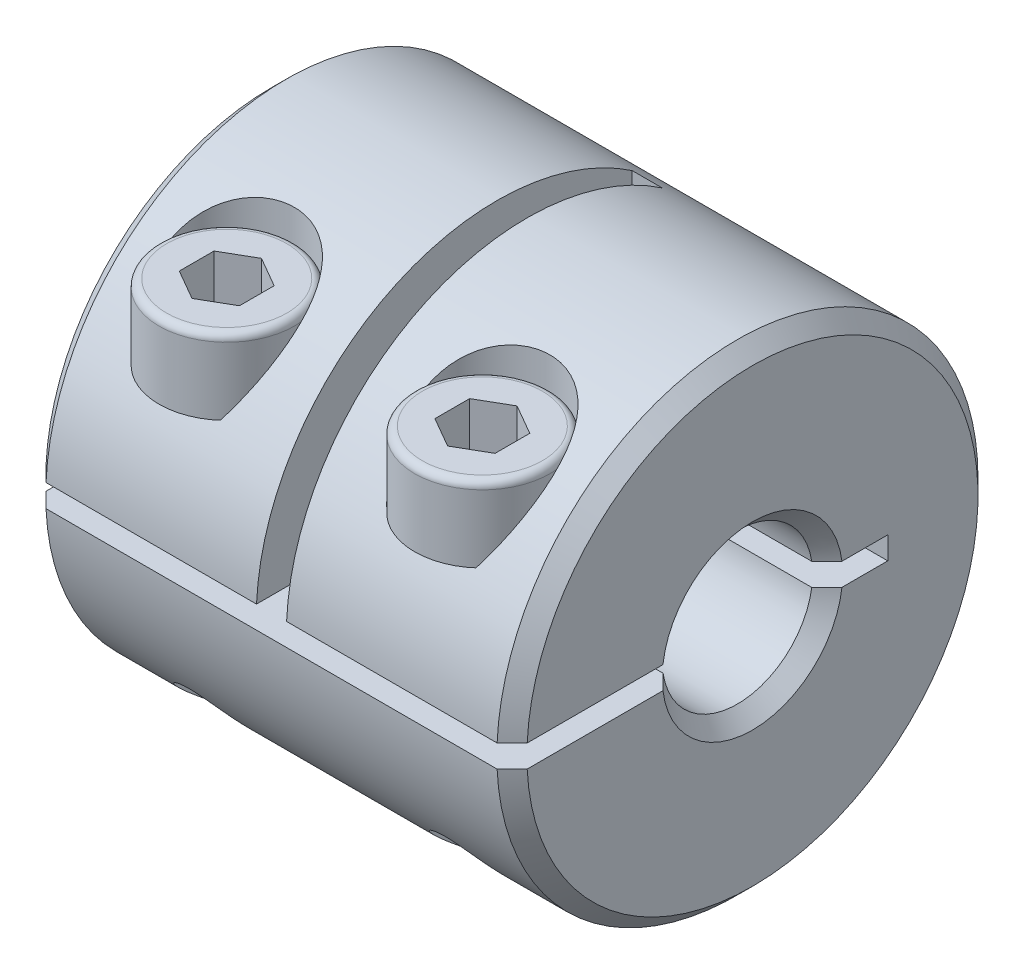
SolidWorks part; units mm, degrees
ref_plane "Front Plane" through (0, 0, 0) normal (0, 0, 1) x (1, 0, 0)
ref_plane "Top Plane" through (0, 0, 0) normal (0, 1, 0) x (1, 0, 0)
ref_plane "Right Plane" through (0, 0, 0) normal (1, 0, 0) x (0, 0, -1)
sketch "Sketch1" plane through (0, 0, 0) normal (1, 0, 0) x (0, 0, -1)
  circle A0 centre (0, 0) radius 8
  dimension "Dim D" = 16
extrude "Boss-Extrude1" add sketch "Sketch1" along normal mid plane 16
sketch "Sketch2" plane through (8, 0, 0) normal (1, 0, 0) x (0, 0, -1)
  circle A0 centre (0, 0) radius 2.5
  dimension "Dim d2" = 5
extrude "Cut-Extrude1" cut sketch "Sketch2" against normal through all
sketch "Sketch5" plane through (8, 0, 0) normal (1, 0, 0) x (0, 0, -1)
  line L0 (0, 0) -> (4.5, 0) construction
  line L1 (-7.9912, 0.375) -> (4.5, 0.375)
  line L2 (2.5, 0.375) -> (2.5, -0.375) construction
  line L3 (-7.9912, -0.375) -> (4.5, -0.375)
  line L4 (4.5, 0.375) -> (4.5, -0.375)
  circle A0 centre (0, 0) radius 8 construction
  arc A1 (-7.9912, 0.375) -> (-7.9912, -0.375) centre (0, 0) ccw
  circle A2 centre (0, 0) radius 2.5 construction
  dimension "D1" = 0.75
  dimension "D2" = 2
extrude "Cut-Extrude2" cut sketch "Sketch5" against normal through all
sketch "Sketch6" plane through (0, 0, -4.5) normal (0, 0, 1) x (1, 0, 0)
  line L0 (-8, -0.375) -> (8, -0.375) construction
  line L1 (-0.5, -0.375) -> (0.5, -0.375)
  line L2 (-0.5, -0.375) -> (-0.5, 8)
  line L3 (-0.5, 8) -> (0.5, 8)
  line L4 (0.5, -0.375) -> (0.5, 8)
  line L5 (8, 8) -> (-8, 8) construction
  line L6 (0, 0) -> (0, 8) construction
  line L7 (8, -8) -> (8, 8) construction
  dimension "Dim L2" = 7.5
extrude "Cut-Extrude3" cut sketch "Sketch6" along normal through all
sketch "Sketch7" plane through (0, -0.375, 0) normal (0, 1, 0) x (1, 0, 0)
  line L0 (4.25, -2.4717) -> (4.25, -7.9912) construction
  line L1 (8, -2.4717) -> (0.5, -2.4717) construction
  line L2 (0.5, -7.9912) -> (8, -7.9912) construction
  line L3 (8, -7.9912) -> (8, 8) construction
  circle A0 centre (4.25, -5.2315) radius 1.25
  dimension "Dim M" = 2.5
  dimension "Dim L1" = 3.75
extrude "Cut-Extrude4" cut sketch "Sketch7" against normal through all and the other way through all
ref_plane "Plane1" through (0, 8, 0) normal (0, 1, 0) x (-1, 0, 0)
ref_plane "Plane2" through (0, 4, 0) normal (0, 1, 0) x (-1, 0, 0)
sketch "Sketch8" plane through (0, 4, 0) normal (0, 1, 0) x (-1, 0, 0)
  circle A0 centre (-4.25, 5.2315) radius 2.25
  dimension "Dim bolt diameter" = 4.5
extrude "Cut-Extrude5" cut sketch "Sketch8" along normal through all
mirror "Mirror1" about plane through (0, 0, 0) normal (1, 0, 0) of "Cut-Extrude5", "Cut-Extrude4"
ref_plane "Plane4" through (0, -8, 0) normal (0, -1, 0) x (1, 0, 0)
ref_plane "Plane5" through (0, -4, 0) normal (0, -1, 0) x (1, 0, 0)
sketch "Sketch9" plane through (0, 4, 0) normal (0, 1, 0) x (1, 0, 0)
  circle A0 centre (4.25, -5.2315) radius 2.25
  circle A1 centre (4.25, -5.2315) radius 2.25 construction
extrude "Boss-Extrude2" add sketch "Sketch9" along normal blind 2.5 separate body
sketch "Sketch10" plane through (0, 6.5, 0) normal (0, 1, 0) x (1, 0, 0)
  circle A0 centre (4.25, -5.2315) radius 1.25 construction
  circle A1 centre (4.25, -5.2315) radius 1.25
extrude "Boss-Extrude3" add sketch "Sketch10" against normal up to surface (10.5 mm away) up to plane "Plane5"
fillet "Fillet1" radius 0.25 2 edges at (4.25, -4, 3.9815) (4.25, 6.5, 7.4815)
sketch "Sketch11" plane through (0, 6.5, 0) normal (0, 1, 0) x (1, 0, 0)
  line L1 (4.25, -4.0768) -> (3.25, -4.6541)
  line L2 (3.25, -4.6541) -> (3.25, -5.8088)
  line L3 (3.25, -5.8088) -> (4.25, -6.3862)
  line L4 (4.25, -6.3862) -> (5.25, -5.8088)
  line L5 (5.25, -5.8088) -> (5.25, -4.6541)
  line L6 (5.25, -4.6541) -> (4.25, -4.0768)
  circle A0 centre (4.25, -5.2315) radius 1 construction
  dimension "Dim hex width" = 2
extrude "Cut-Extrude6" cut sketch "Sketch11" against normal blind 2
mirror "Mirror2" about plane through (0, 0, 0) normal (1, 0, 0) of bodies 111
chamfer "Chamfer1" distance 0.5 angle 45 6 edges at (-8, 0, -8) (8, 0, -8) (-8, 2.5, 0) (-8, -2.5, 0) (8, -2.5, 0) (8, 2.5, 0)
